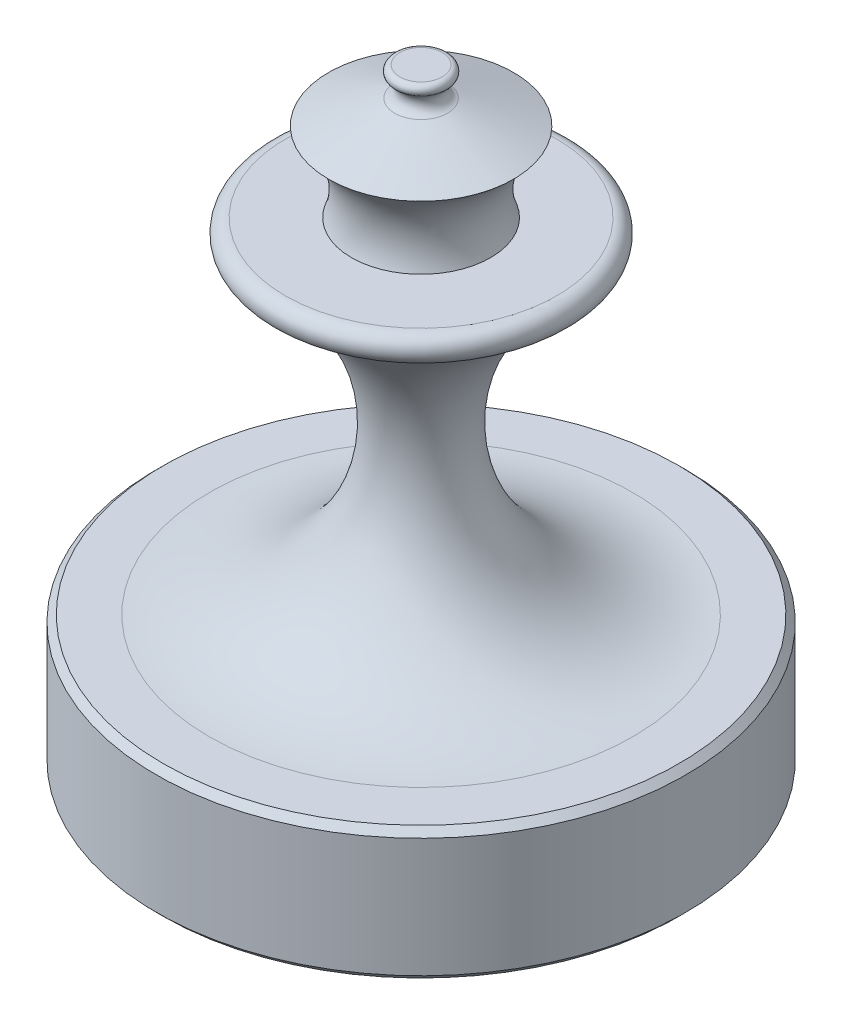
SolidWorks part; units mm, degrees
ref_plane "Face" through (0, 0, 0) normal (0, 0, 1) x (1, 0, 0)
ref_plane "Dessus" through (0, 0, 0) normal (0, 1, 0) x (1, 0, 0)
ref_plane "Droite" through (0, 0, 0) normal (1, 0, 0) x (0, 0, -1)
sketch "Esquisse1" plane through (0, 0, 0) normal (0, 0, 1) x (1, 0, 0)
  line L0 (0, 0) -> (0, 180) construction
  line L1 (0, 0) -> (-80, 0) construction
  line L2 (-51.3099, 130) -> (-26.3099, 130)
  line L3 (0, 180) -> (-8, 180)
  line L4 (-9.9608, 169.0769) -> (-34.9608, 160)
  line L5 (-80, 0) -> (0, 0)
  line L6 (0, 180) -> (0, 0)
  arc A0 (-80, 0) -> (-53.4717, 120.2046) centre (-80, 63.0296) ccw
  arc A1 (-53.4717, 120.2046) -> (-51.3099, 130) centre (-51.3099, 124.8637) cw
  arc A2 (-8, 180) -> (-9.1398, 176.1714) centre (-8, 177.916) ccw
  arc A3 (-9.1398, 176.1714) -> (-9.9608, 169.0769) centre (-11.3232, 172.8293) cw
  arc A4 (-26.3099, 130) -> (-34.9608, 160) centre (-50.0763, 139.3939) ccw
  point P3 (0, 180)
  point P16 (0, 0)
  dimension "D5" = 25
  dimension "D6" = 25
  dimension "D1" = 180
  dimension "D2" = 80
  dimension "D3" = 8
  dimension "D4" = 130
  dimension "D7" = 30
revolve "Révolution2" add sketch "Esquisse1" angle 360 about L6
sketch "Esquisse2" plane through (0, 0, 0) normal (0, -1, 0) x (1, 0, 0)
  circle A0 centre (0, 0) radius 100
  dimension "D1" = 200
extrude "Extrusion1" add sketch "Esquisse2" along normal blind 50
chamfer "Chanfrein1" distance 2.5 angle 45 2 edges at (0, -50, -100) (0, 0, -100)
